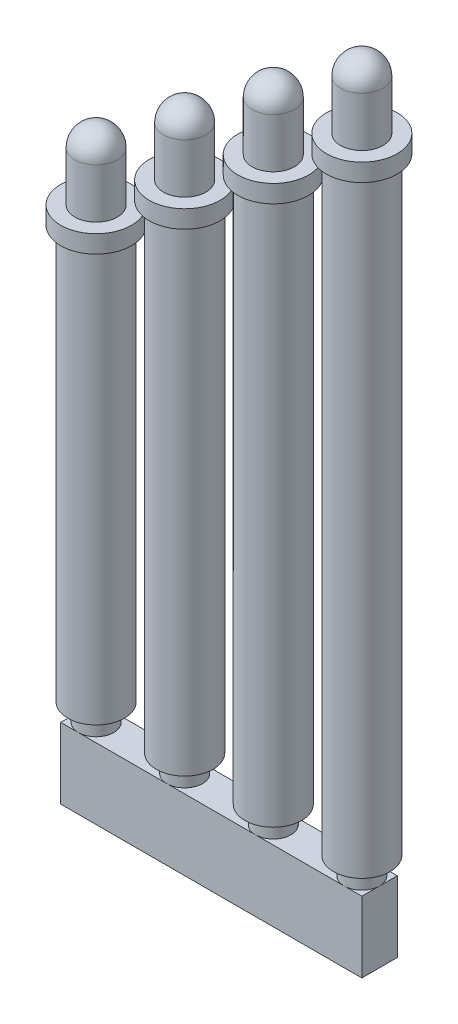
SolidWorks part; units mm, degrees
ref_plane "Front Plane" through (0, 0, 0) normal (0, 0, 1) x (1, 0, 0)
ref_plane "Top Plane" through (0, 0, 0) normal (0, 1, 0) x (1, 0, 0)
ref_plane "Right Plane" through (0, 0, 0) normal (1, 0, 0) x (0, 0, -1)
sketch "Sketch10" plane through (0, 0, 0) normal (0, 0, 1) x (1, 0, 0)
  line L0 (0, 0) -> (-0.5, 0)
  line L1 (-0.5, 0) -> (-0.5, 0.5)
  line L2 (-0.5, 0.5) -> (-0.8, 0.5)
  line L3 (-1, 12.15) -> (-1, 12.65)
  line L4 (-1, 12.65) -> (-0.6, 12.65)
  line L5 (-0.6, 12.65) -> (-0.6, 14.65)
  line L6 (-0.6, 14.65) -> (0, 14.65)
  line L7 (0, 14.65) -> (0, 0)
  line L8 (-1, 12.15) -> (-0.8, 12.15)
  line L9 (-0.8, 12.15) -> (-0.8, 0.5)
  dimension "D1" = 0.5
  dimension "D2" = 1
  dimension "D3" = 0.6
  dimension "D4" = 0.5
  dimension "D5" = 2
  dimension "D6" = 14.65
  dimension "D7" = 0.8
  dimension "D8" = 0.5
revolve "Revolve1" add sketch "Sketch10" angle 360 about L7
sketch "Sketch11" plane through (0, 0, 0) normal (0, 0, 1) x (1, 0, 0)
  line L0 (2.5, 0) -> (2, 0)
  line L1 (2, 0) -> (2, 0.5)
  line L2 (2, 0.5) -> (1.7, 0.5)
  line L3 (1.5, 14.01) -> (1.5, 14.51)
  line L4 (1.5, 14.51) -> (1.9, 14.51)
  line L5 (1.9, 14.51) -> (1.9, 16.51)
  line L6 (1.9, 16.51) -> (2.5, 16.51)
  line L7 (2.5, 16.51) -> (2.5, 0)
  line L8 (-0.5, 0) -> (0.5, 0) construction
  line L9 (1.5, 14.01) -> (1.7, 14.01)
  line L10 (1.7, 14.01) -> (1.7, 0.5)
  dimension "D1" = 0.5
  dimension "D2" = 0.5
  dimension "D3" = 2
  dimension "D4" = 0.6
  dimension "D5" = 16.51
  dimension "D6" = 1
  dimension "D7" = 2.5
  dimension "D8" = 0.5
  dimension "D9" = 0.8
revolve "Revolve2" add sketch "Sketch11" angle 360 about L7
sketch "Sketch12" plane through (0, 0, 0) normal (0, 0, 1) x (1, 0, 0)
  line L0 (5, 0) -> (4.5, 0)
  line L1 (4.5, 0) -> (4.5, 0.5)
  line L2 (4.5, 0.5) -> (4.2, 0.5)
  line L3 (4, 15.88) -> (4, 16.38)
  line L4 (4, 16.38) -> (4.4, 16.38)
  line L5 (4.4, 16.38) -> (4.4, 18.38)
  line L6 (4.4, 18.38) -> (5, 18.38)
  line L7 (5, 18.38) -> (5, 0)
  line L8 (-0.5, 0) -> (0.5, 0) construction
  line L9 (4, 15.88) -> (4.2, 15.88)
  line L10 (4.2, 15.88) -> (4.2, 0.5)
  dimension "D1" = 0.5
  dimension "D2" = 1
  dimension "D3" = 0.6
  dimension "D4" = 0.5
  dimension "D5" = 2
  dimension "D6" = 18.38
  dimension "D7" = 5
  dimension "D8" = 0.8
  dimension "D9" = 0.5
revolve "Revolve3" add sketch "Sketch12" angle 360 about L7
sketch "Sketch13" plane through (0, 0, 0) normal (0, 0, 1) x (1, 0, 0)
  line L0 (7.5, 0) -> (7, 0)
  line L1 (7, 0) -> (7, 0.5)
  line L2 (7, 0.5) -> (6.7, 0.5)
  line L3 (6.5, 17.65) -> (6.5, 18.15)
  line L4 (6.5, 18.15) -> (6.9, 18.15)
  line L5 (6.9, 18.15) -> (6.9, 20.15)
  line L6 (6.9, 20.15) -> (7.5, 20.15)
  line L7 (7.5, 20.15) -> (7.5, 0)
  line L8 (-0.5, 0) -> (0.5, 0) construction
  line L9 (6.5, 17.65) -> (6.7, 17.65)
  line L10 (6.7, 17.65) -> (6.7, 0.5)
  dimension "D1" = 0.5
  dimension "D2" = 0.5
  dimension "D3" = 1
  dimension "D4" = 0.6
  dimension "D5" = 2
  dimension "D6" = 20.15
  dimension "D7" = 7.5
  dimension "D8" = 0.8
  dimension "D9" = 0.5
revolve "Revolve4" add sketch "Sketch13" angle 360 about L7
fillet "Fillet2" radius 0.6 1 edges at (-0.6, 14.65, 0)
fillet "Fillet3" radius 0.6 1 edges at (1.9, 16.51, 0)
fillet "Fillet4" radius 0.6 1 edges at (4.4, 18.38, 0)
fillet "Fillet5" radius 0.6 1 edges at (6.9, 20.15, 0)
sketch "Sketch14" plane through (0, 0, 0) normal (0, -1, 0) x (1, 0, 0)
  line L1 (-0.5, 0.5) -> (8, 0.5)
  line L2 (-0.5, 0.5) -> (-0.5, -0.5)
  line L3 (-0.5, -0.5) -> (8, -0.5)
  line L4 (8, 0.5) -> (8, -0.5)
  circle A0 centre (0, 0) radius 0.5 construction
  circle A1 centre (0, 0) radius 0.5 construction
  circle A2 centre (7.5, 0) radius 0.5 construction
extrude "Boss-Extrude1" add sketch "Sketch14" along normal blind 2
